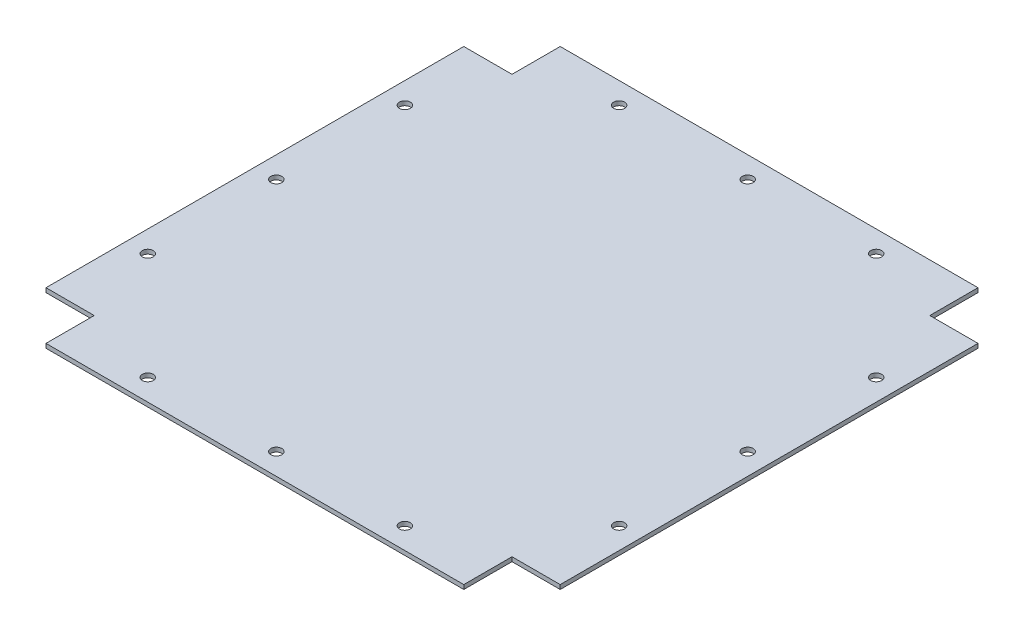
SolidWorks part; units mm, degrees
ref_plane "Front Plane" through (0, 0, 0) normal (0, 0, 1) x (1, 0, 0)
ref_plane "Top Plane" through (0, 0, 0) normal (0, 1, 0) x (1, 0, 0)
ref_plane "Right Plane" through (0, 0, 0) normal (1, 0, 0) x (0, 0, -1)
sketch "Sketch1" plane through (0, 0, 0) normal (0, 1, 0) x (1, 0, 0)
  line L0 (123.825, 152.4) -> (123.825, 123.825)
  line L1 (-123.825, -152.4) -> (123.825, -152.4)
  line L2 (-152.4, -123.825) -> (-152.4, 123.825)
  line L3 (-123.825, 152.4) -> (123.825, 152.4)
  line L4 (152.4, -123.825) -> (152.4, 123.825)
  line L5 (-152.4, -152.4) -> (152.4, 152.4) construction
  line L6 (-152.4, 152.4) -> (152.4, -152.4) construction
  line L7 (123.825, 123.825) -> (152.4, 123.825)
  line L8 (-152.4, -123.825) -> (-123.825, -123.825)
  line L9 (-123.825, -123.825) -> (-123.825, -152.4)
  line L10 (152.4, 0) -> (-152.4, 0) construction
  line L11 (123.825, -123.825) -> (152.4, -123.825)
  line L12 (123.825, -152.4) -> (123.825, -123.825)
  line L13 (-152.4, 123.825) -> (-123.825, 123.825)
  line L14 (-123.825, 123.825) -> (-123.825, 152.4)
  line L15 (123.825, 139.7) -> (-123.825, 139.7) construction
  circle A0 centre (76.2, 139.7) radius 3.2385
  circle A1 centre (0, 139.7) radius 3.2385
  circle A2 centre (-76.2, 139.7) radius 3.2385
  circle A3 centre (-76.2, -139.7) radius 3.2385
  circle A4 centre (0, -139.7) radius 3.2385
  circle A5 centre (76.2, -139.7) radius 3.2385
  circle A6 centre (139.7, -76.2) radius 3.2385
  circle A7 centre (139.7, 0) radius 3.2385
  circle A8 centre (139.7, 76.2) radius 3.2385
  circle A9 centre (-139.7, 76.2) radius 3.2385
  circle A10 centre (-139.7, 0) radius 3.2385
  circle A11 centre (-139.7, -76.2) radius 3.2385
  point P0 (0, 0)
  dimension "D4" = 6.477
  dimension "D1" = 304.8
  dimension "D2" = 28.575
  dimension "D3" = 12.7
  dimension "D5" = 76.2
  dimension "D6" = 76.2
extrude "Boss-Extrude1" add sketch "Sketch1" along normal blind 2.54
